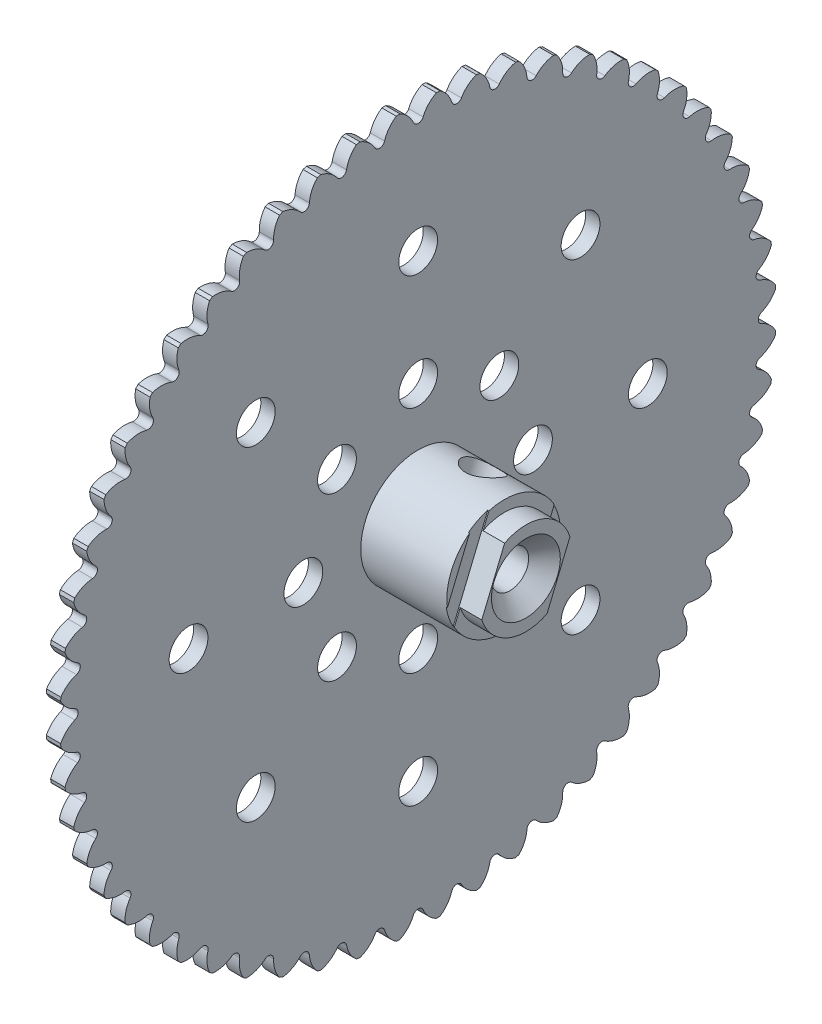
SolidWorks part; units mm, degrees
material "Brass"
ref_plane "Front Plane" through (0, 0, 0) normal (0, 0, 1) x (1, 0, 0)
ref_plane "Top Plane" through (0, 0, 0) normal (0, 1, 0) x (1, 0, 0)
ref_plane "Right Plane" through (0, 0, 0) normal (1, 0, 0) x (0, 0, -1)
sketch "Sketch1" plane through (0, 0, 0) normal (1, 0, 0) x (0, 0, -1)
  circle A0 centre (0, 0) radius 39.5986
  dimension "D1" = 79.1972
extrude "Boss-Extrude1" add sketch "Sketch1" along normal blind 1.5875
sketch "Sketch2" plane through (1.5875, 0, 0) normal (1, 0, 0) x (0, 0, -1)
  circle A0 centre (0, 0) radius 12.7 construction
  circle A1 centre (0, 12.7) radius 2.1463
  circle A2 centre (0, 25.4) radius 2.1463
  circle A3 centre (0, 0) radius 25.4 construction
  dimension "D1" = 25.4
  dimension "D2" = 4.2926
  dimension "D3" = 50.8
extrude "Cut-Extrude1" cut sketch "Sketch2" against normal blind 1.5875
pattern_circular "CirPattern1" count 8 over 360 about axis through (0, 0, 0) along (1, 0, 0) of "Cut-Extrude1"
sketch "Sketch4" plane through (1.5875, 0, 0) normal (1, 0, 0) x (0, 0, -1)
  line L0 (0, 37.6174) -> (0, 39.5986) construction
  line L1 (0, 0.8731) -> (0, -0.8731) construction
  line L2 (0, 0) -> (-2.0174, 39.5472) construction
  line L3 (0, 0) -> (2.4232, 39.5244) construction
  arc A0 (-2.0174, 39.5472) -> (-0.5366, 37.9706) centre (-3.4529, 36.7152) cw
  circle A1 centre (0, 0) radius 39.5986 construction
  arc A2 (-0.5366, 37.9706) -> (0.5366, 37.9706) centre (0, 38.2016) ccw
  arc A3 (0.5366, 37.9706) -> (2.0174, 39.5472) centre (3.4529, 36.7152) cw
  arc A4 (-2.0174, 39.5472) -> (2.4232, 39.5244) centre (0, 0) cw
  circle M13 centre (0, 0) radius 39.5986
  dimension "D1" = 0.5842
  dimension "D2" = 3.175
  dimension "D3" = 1.9812
  dimension "D4" = 6.429
  dimension "D5" = 0.4064
extrude "Cut-Extrude2" cut sketch "Sketch4" against normal blind 1.5875 contours A2 A3 A0 M13
pattern_circular "CirPattern2" count 56 over 360 about axis through (0, 0, 0) along (1, 0, 0) of "Cut-Extrude2"
sketch "Sketch7" plane through (1.5875, 0, 0) normal (1, 0, 0) x (0, 0, -1)
  circle A0 centre (0, 0) radius 6.35
  dimension "D1" = 12.7
extrude "Boss-Extrude3" add sketch "Sketch7" along normal blind 9.525
sketch "Sketch8" plane through (11.1125, 0, 0) normal (1, 0, 0) x (0, 0, -1)
  line L0 (-4.877, -1.5525) -> (-2.3507, 4.5463)
  line L1 (2.3507, -4.5463) -> (4.877, 1.5525)
  line L3 (0, 5.1181) -> (0, -5.1181) construction
  arc A0 (-4.877, -1.5525) -> (2.3507, -4.5463) centre (0, 0) ccw
  arc A1 (4.877, 1.5525) -> (-2.3507, 4.5463) centre (0, 0) ccw
  dimension "D3" = 10.2362
  dimension "D1" = 22.5
  dimension "D2" = 7.8232
extrude "Boss-Extrude4" add sketch "Sketch8" along normal blind 2.3876
sketch "Sketch9" plane through (13.5001, 0, 0) normal (1, 0, 0) x (0, 0, -1)
  circle A0 centre (0, 0) radius 2.0574
  dimension "D1" = 4.1148
extrude "Cut-Extrude3" cut sketch "Sketch9" against normal through all contours A0
sketch "Sketch10" plane through (11.1125, 0, 0) normal (1, 0, 0) x (0, 0, -1)
  line L0 (-5.5281, -3.1245) -> (-1.6996, 6.1183)
  line L1 (-2.3507, 4.5463) -> (-4.877, -1.5525) construction
  line L2 (-6.2923, -0.8542) -> (-3.8453, 5.0534)
  line L3 (-3.9537, -9.545) -> (3.9537, 9.545) construction
  line L4 (3.8453, -5.0534) -> (6.2923, 0.8542)
  line L5 (1.6996, -6.1183) -> (5.5281, 3.1245)
  circle A0 centre (0, 0) radius 6.35 construction
  circle A1 centre (0, 0) radius 6.35 construction
  arc A4 (-1.6996, 6.1183) -> (-3.8453, 5.0534) centre (0, 0) ccw
  arc A5 (-5.5281, -3.1245) -> (-6.2923, -0.8542) centre (0, 0) cw
  arc A6 (1.6996, -6.1183) -> (3.8453, -5.0534) centre (0, 0) ccw
  arc A7 (5.5281, 3.1245) -> (6.2923, 0.8542) centre (0, 0) cw
  point P17 (0, 0)
  dimension "D1" = 1.5748
extrude "Cut-Extrude4" cut sketch "Sketch10" against normal blind 0.127
sketch "Sketch11" plane through (0, 0, 0) normal (0, 0, 1) x (1, 0, 0)
  line L3 (13.5001, -3.81) -> (13.5001, 3.81)
  line L5 (13.5001, 4.5463) -> (13.5001, -1.5525) construction
  line L6 (13.5001, 3.81) -> (9.6901, 0)
  line L7 (9.6901, 0) -> (13.5001, -3.81)
  line L8 (13.5001, 0) -> (9.6901, 0) construction
  point P3 (13.5001, 0)
  dimension "D1" = 90
  dimension "D2" = 7.62
revolve "Cut-Revolve4" cut sketch "Sketch11" angle 360 about L8
ref_plane "Plane1" through (0, 0, 0) normal (0, -0.3827, -0.9239) x (-1, 0, 0)
sketch "Sketch12" plane through (0, 0, 0) normal (0, -0.3827, -0.9239) x (-1, 0, 0)
  line L0 (-6.35, -6.35) -> (-6.35, 6.35)
  line L1 (-1.5875, 6.35) -> (-11.1125, 6.35) construction
  line L2 (-8.3344, -6.35) -> (-8.3344, 6.35)
  line L3 (-11.1125, -6.35) -> (-1.5875, -6.35) construction
  line L4 (-8.3344, 6.35) -> (-6.35, 6.35)
  line L5 (-8.3344, -6.35) -> (-6.35, -6.35)
  point P5 (-6.35, 0)
  dimension "D1" = 4.7625
  dimension "D2" = 1.9844
revolve "Cut-Revolve5" cut sketch "Sketch12" angle 360 about L0
